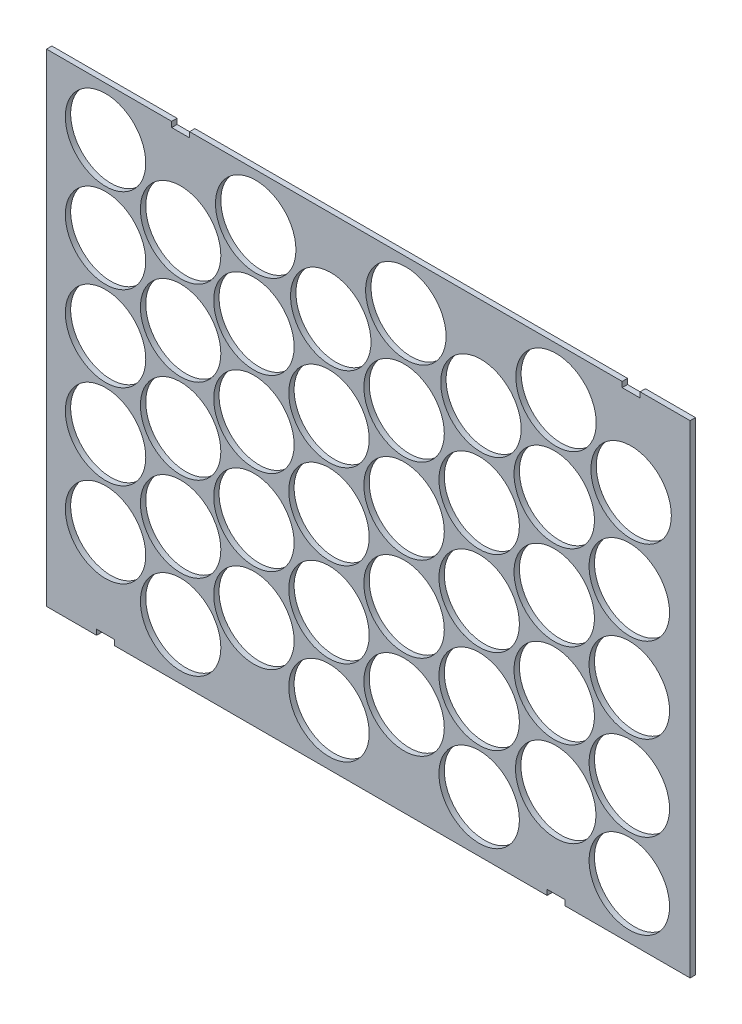
SolidWorks part; units mm, degrees
material "ABS PC"
ref_plane "Alzado" through (0, 0, 0) normal (0, 0, 1) x (1, 0, 0)
ref_plane "Planta" through (0, 0, 0) normal (0, 1, 0) x (1, 0, 0)
ref_plane "Vista lateral" through (0, 0, 0) normal (1, 0, 0) x (0, 0, -1)
sketch "Croquis2" plane through (0, 0, 0) normal (0, 0, 1) x (1, 0, 0)
  line L0 (-78.0327, 45.4815) -> (-8.0327, 45.4815)
  line L1 (1.9673, 45.4815) -> (243.9673, 45.494)
  line L2 (-78.0327, 45.4815) -> (-78.0327, -224.5185)
  line L3 (-78.0327, -224.5185) -> (-50.0327, -224.5185)
  line L4 (281.9673, 45.4815) -> (281.9673, -224.5185)
  line L5 (-50.0327, -221.5185) -> (-40.0327, -221.5185)
  line L6 (-50.0327, -221.5185) -> (-50.0327, -224.5185)
  line L7 (-40.0327, -224.5185) -> (201.9673, -224.5483)
  line L8 (-40.0327, -221.5185) -> (-40.0327, -224.5185)
  line L9 (-8.0327, 45.4815) -> (-8.0327, 42.4815)
  line L10 (-8.0327, 42.4815) -> (1.9673, 42.4815)
  line L11 (1.9673, 45.4815) -> (1.9673, 42.4815)
  line L12 (243.9673, 45.494) -> (243.9673, 45.4806)
  line L13 (243.9673, 45.4806) -> (243.9673, 42.4806)
  line L14 (243.9673, 42.4806) -> (253.9673, 42.4806)
  line L15 (253.9673, 45.4806) -> (253.9673, 42.4806)
  line L16 (201.9673, -221.5483) -> (211.9673, -221.5483)
  line L17 (201.9673, -221.5483) -> (201.9673, -224.5483)
  line L19 (211.9673, -221.5483) -> (211.9673, -224.5483)
  line L20 (253.9673, 45.4806) -> (281.9673, 45.4815)
  line L21 (211.9673, -224.5483) -> (281.9673, -224.5185)
  circle A0 centre (-45.0327, 17.9815) radius 22.5
  circle A1 centre (-45.0327, -29.5185) radius 22.5
  circle A2 centre (-45.0327, -77.0185) radius 22.5
  circle A3 centre (-45.0327, -124.5185) radius 22.5
  circle A4 centre (-45.0327, -172.0185) radius 22.5
  circle A5 centre (-3.0327, -5.7685) radius 22.5
  circle A6 centre (38.9673, 17.9815) radius 22.5
  circle A7 centre (80.9673, -5.7685) radius 22.5
  circle A8 centre (122.9673, 17.9815) radius 22.5
  circle A9 centre (164.9673, -5.7685) radius 22.5
  circle A10 centre (-3.0327, -53.2685) radius 22.5
  circle A11 centre (-3.0327, -100.7685) radius 22.5
  circle A12 centre (-3.0327, -148.2685) radius 22.5
  circle A13 centre (-3.0327, -195.7685) radius 22.5
  circle A14 centre (37.9673, -29.5185) radius 22.5
  circle A15 centre (37.9673, -77.0185) radius 22.5
  circle A16 centre (37.9673, -124.5185) radius 22.5
  circle A17 centre (37.9673, -172.0185) radius 22.5
  circle A18 centre (79.9673, -53.2685) radius 22.5
  circle A19 centre (79.9673, -100.7685) radius 22.5
  circle A20 centre (79.9673, -148.2685) radius 22.5
  circle A21 centre (79.9673, -195.7685) radius 22.5
  circle A22 centre (121.9673, -29.5185) radius 22.5
  circle A23 centre (163.9673, -53.2685) radius 22.5
  circle A24 centre (121.9673, -77.0185) radius 22.5
  circle A25 centre (163.9673, -100.7685) radius 22.5
  circle A26 centre (121.9673, -124.5185) radius 22.5
  circle A27 centre (121.9673, -172.0185) radius 22.5
  circle A28 centre (163.9673, -148.2685) radius 22.5
  circle A29 centre (163.9673, -195.7685) radius 22.5
  circle A30 centre (206.9673, 18.0715) radius 22.5
  circle A31 centre (205.9673, -29.5185) radius 22.5
  circle A32 centre (205.9673, -77.0185) radius 22.5
  circle A33 centre (205.9673, -124.5185) radius 22.5
  circle A34 centre (206.7962, -171.9285) radius 22.5
  circle A35 centre (248.9673, -5.7685) radius 22.5
  circle A36 centre (247.9673, -53.2685) radius 22.5
  circle A37 centre (247.9673, -100.7685) radius 22.5
  circle A38 centre (247.9673, -148.2685) radius 22.5
  circle A39 centre (247.9673, -195.7685) radius 22.5
  point P100 (-45.0327, -221.5185)
  point P101 (206.9673, -221.5483)
  point P102 (248.9673, 42.4806)
  point P103 (-3.0327, 42.4815)
  dimension "D3" = 45
  dimension "D4" = 33
  dimension "D2" = 270
  dimension "D5" = 3
  dimension "D6" = 47.5
  dimension "D7" = 47.5
  dimension "D8" = 47.5
  dimension "D9" = 47.5
  dimension "D10" = 3
  dimension "D11" = 42
  dimension "D12" = 42
  dimension "D13" = 42
  dimension "D14" = 42
  dimension "D15" = 42
  dimension "D16" = 47.5
  dimension "D17" = 47.5
  dimension "D18" = 47.5
  dimension "D19" = 47.5
  dimension "D20" = 42
  dimension "D21" = 42
  dimension "D22" = 33
  dimension "D23" = 360
  dimension "D24" = 33
  dimension "D25" = 75
  dimension "D26" = 33
  dimension "D27" = 75
  dimension "D28" = 3
  dimension "D29" = 3
extrude "Saliente-Extruir1" add sketch "Croquis2" along normal blind 3
